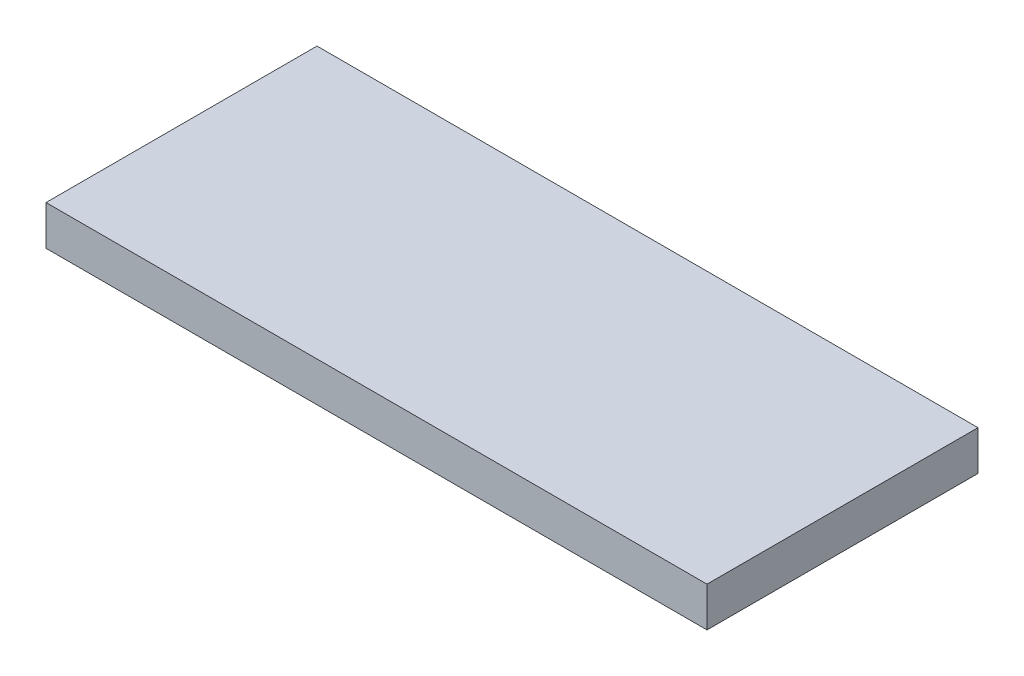
SolidWorks part; units mm, degrees
ref_plane "Plan de face" through (0, 0, 0) normal (0, 0, 1) x (1, 0, 0)
ref_plane "Plan de dessus" through (0, 0, 0) normal (0, 1, 0) x (1, 0, 0)
ref_plane "Plan de droite" through (0, 0, 0) normal (1, 0, 0) x (0, 0, -1)
sketch "Esquisse1" plane through (0, 0, 0) normal (0, 1, 0) x (1, 0, 0)
  line L0 (-41.8571, 0) -> (45.2857, 0) construction
  line L1 (0, 28.0714) -> (0, -24.6429) construction
  line L2 (-36.2857, 22.2143) -> (63.7143, 22.2143)
  line L3 (-36.2857, 22.2143) -> (-36.2857, -18.7857)
  line L4 (63.7143, 22.2143) -> (63.7143, -18.7857)
  line L5 (-36.2857, -18.7857) -> (63.7143, -18.7857)
  dimension "D1" = 41
  dimension "D2" = 100
extrude "Boss.-Extru.1" add sketch "Esquisse1" along normal blind 6
